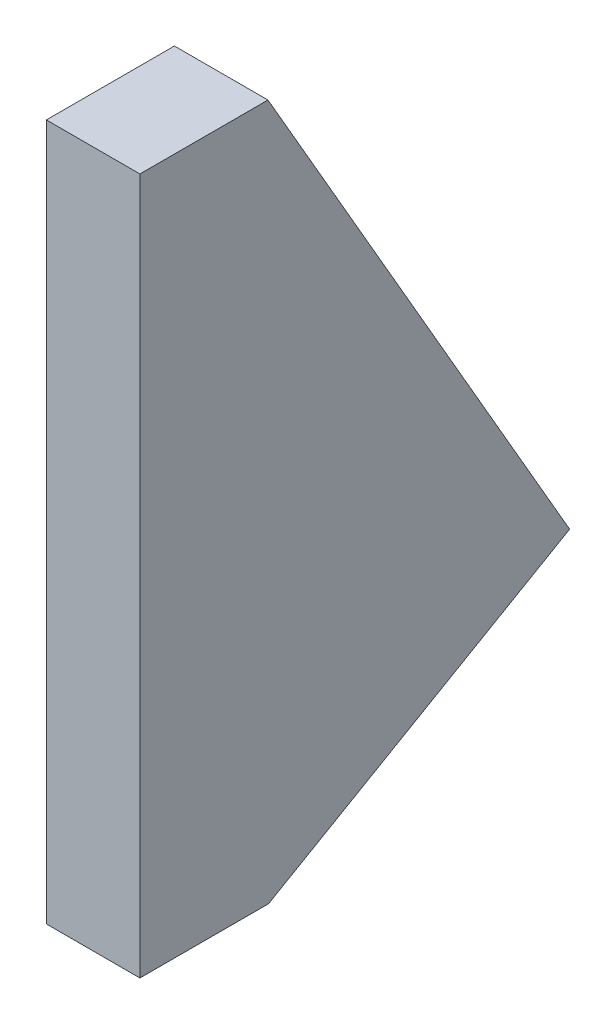
SolidWorks part; units mm, degrees
ref_plane "Front Plane" through (0, 0, 0) normal (0, 0, 1) x (1, 0, 0)
ref_plane "Top Plane" through (0, 0, 0) normal (0, 1, 0) x (1, 0, 0)
ref_plane "Right Plane" through (0, 0, 0) normal (1, 0, 0) x (0, 0, -1)
sketch "Sketch1" plane through (0, 0, 0) normal (1, 0, 0) x (0, 0, -1)
  line L0 (0, -11.8775) -> (0, 11.8775)
  line L3 (14.7312, -5.9387) -> (4.445, 11.8775)
  line L4 (4.445, 11.8775) -> (0, 11.8775)
  line L5 (0, -11.8775) -> (4.445, -11.8775)
  line L6 (4.445, -11.8775) -> (14.7312, -5.9387)
  line L7 (4.428, -11.814) -> (14.6445, -5.9155)
  line L8 (14.6445, -5.9155) -> (4.4083, 11.814)
  line L9 (4.4083, 11.814) -> (0.0635, 11.814)
  line L10 (0.0635, -11.814) -> (0.0635, 11.814)
  line L11 (0.0635, -11.814) -> (4.428, -11.814)
  point P8 (0, 0)
  dimension "D1" = 4.445
  dimension "D2" = 4.445
  dimension "D3" = 11.8775
  dimension "D4" = 23.755
  dimension "D5" = 20.5724
  dimension "D6" = 0.0635
extrude "Boss-Extrude1" add sketch "Sketch1" along normal blind 3.175 contours L7 L8 L9 L10 L11
